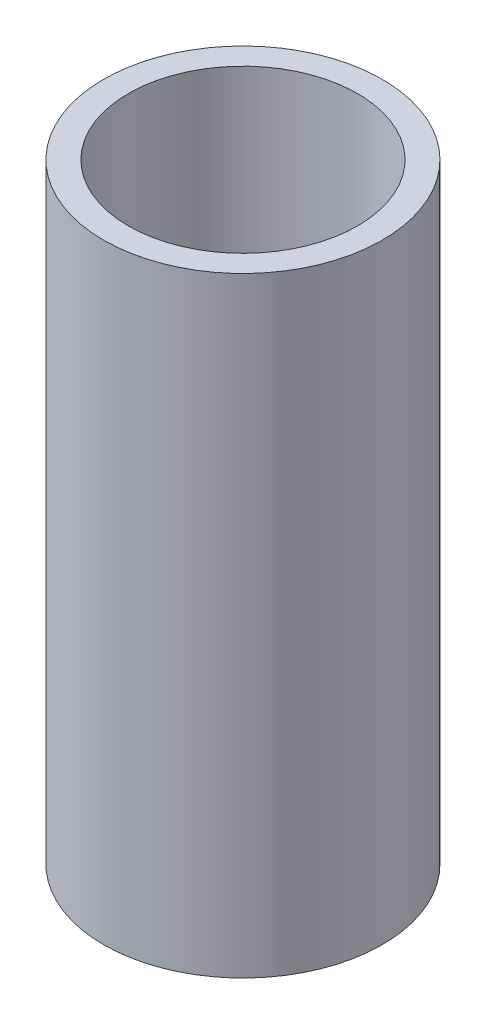
SolidWorks part; units mm, degrees
ref_plane "Front Plane" through (0, 0, 0) normal (0, 0, 1) x (1, 0, 0)
ref_plane "Top Plane" through (0, 0, 0) normal (0, 1, 0) x (1, 0, 0)
ref_plane "Right Plane" through (0, 0, 0) normal (1, 0, 0) x (0, 0, -1)
sketch "Sketch1" plane through (0, 0, 0) normal (0, 1, 0) x (1, 0, 0)
  circle A0 centre (0, 0) radius 39.5
  dimension "D1" = 79
extrude "Boss-Extrude1" add sketch "Sketch1" along normal blind 173
sketch "Sketch2" plane through (0, 173, 0) normal (0, 1, 0) x (1, 0, 0)
  circle A0 centre (0, 0) radius 32.5
  circle A1 centre (0, 0) radius 39.5 construction
  dimension "D1" = 7
extrude "Cut-Extrude1" cut sketch "Sketch2" against normal blind 125
